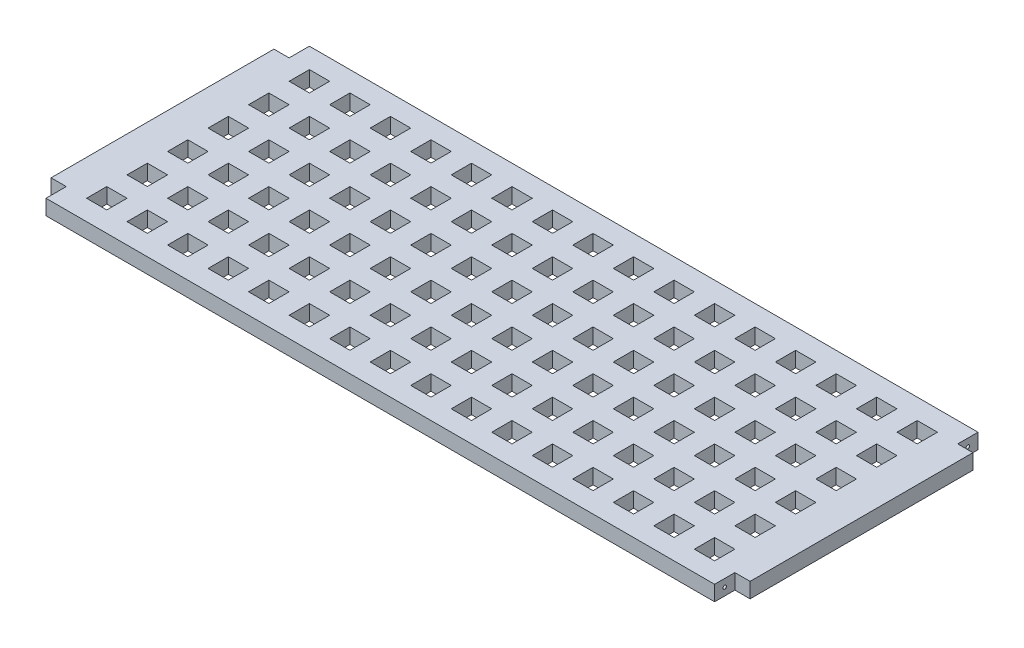
SolidWorks part; units mm, degrees
ref_plane "Front Plane" through (0, 0, 0) normal (0, 0, 1) x (1, 0, 0)
ref_plane "Top Plane" through (0, 0, 0) normal (0, 1, 0) x (1, 0, 0)
ref_plane "Right Plane" through (0, 0, 0) normal (1, 0, 0) x (0, 0, -1)
sketch "Sketch1" plane through (0, 0, 0) normal (0, 1, 0) x (1, 0, 0)
  line L0 (-373.3767, 133.8437) -> (-358.3767, 133.8437)
  line L1 (-358.3767, 133.8437) -> (-358.3767, 153.8437)
  line L2 (-358.3767, 153.8437) -> (301.6233, 153.8437)
  line L3 (301.6233, 153.8437) -> (301.6233, 133.8437)
  line L4 (301.6233, 133.8437) -> (316.6233, 133.8437)
  line L5 (316.6233, 133.8437) -> (316.6233, -86.1563)
  line L6 (316.6233, -86.1563) -> (301.6233, -86.1563)
  line L7 (301.6233, -86.1563) -> (301.6233, -106.1563)
  line L8 (301.6233, -106.1563) -> (-358.3767, -106.1563)
  line L9 (-358.3767, -106.1563) -> (-358.3767, -86.1563)
  line L10 (-358.3767, -86.1563) -> (-373.3767, -86.1563)
  line L11 (-373.3767, -86.1563) -> (-373.3767, 133.8437)
  dimension "D1" = 660
  dimension "D2" = 20
  dimension "D3" = 20
  dimension "D4" = 15
  dimension "D5" = 15
  dimension "D6" = 220
  dimension "D7" = 15
  dimension "D8" = 20
  dimension "D9" = 220
  dimension "D10" = 660
extrude "Boss-Extrude2" add sketch "Sketch1" against normal blind 15
sketch "Sketch2" plane through (0, 0, 0) normal (0, 1, 0) x (1, 0, 0)
  line L0 (301.6233, 153.8437) -> (-358.3767, 153.8437) construction
  line L1 (-338.3767, 133.8437) -> (-318.3767, 133.8437)
  line L2 (-338.3767, 133.8437) -> (-338.3767, 113.8437)
  line L3 (-338.3767, 113.8437) -> (-318.3767, 113.8437)
  line L4 (-318.3767, 133.8437) -> (-318.3767, 113.8437)
  line L5 (-373.3767, 133.8437) -> (-373.3767, -86.1563) construction
  dimension "D1" = 20
  dimension "D2" = 35
  dimension "D3" = 20
  dimension "D4" = 20
extrude "Cut-Extrude1" cut sketch "Sketch2" against normal blind 15
pattern_linear "LPattern1" count 16 spacing 40 along (1, 0, 0) count 6 spacing 40 along (0, 0, 1) of "Cut-Extrude1"
sketch "Sketch7" plane through (301.6233, 0, 0) normal (1, 0, 0) x (0, 0, -1)
  line L0 (153.8437, -15) -> (153.8437, 0) construction
  line L1 (153.8437, 0) -> (133.8437, 0) construction
  line L2 (-106.1563, -15) -> (-106.1563, 0) construction
  point P1 (143.8437, -7.5)
  point P2 (-96.1563, -7.5)
  point P3 (143.8437, -7.5)
  point P6 (153.8437, -7.5)
  dimension "D1" = 10
  dimension "D2" = 7.5
  dimension "D3" = 10
hole_wizard "M3 Clearance Hole2" positions "3DSketch2" profile "Sketch9" hole size "M3" standard "ANSI Metric"
sketch3d "3DSketch2"
  point P1 (301.6233, -7.5, -143.8437)
  point P4 (301.6233, -7.5, 96.1563)
sketch "Sketch9" plane through (301.6233, -7.5, -143.8437) normal (0, 1, 0) x (0, 0, -1)
  line L0 (0, 0) -> (0, 15)
  line L1 (0, 15) -> (1.7, 13.9785)
  line L2 (1.7, 13.9785) -> (1.7, 0.025)
  line L3 (1.7, 0.025) -> (1.725, 0)
  line L5 (1.725, 0) -> (0, 0)
  line L6 (-1.7, 0.025) -> (-1.725, 0) construction
  line L10 (0, 15) -> (-1.7, 13.9785) construction
  line L11 (0, -6.35) -> (0, 107.95) construction
  dimension "Hole Dia." = 3.4
  dimension "Hole Depth" = 15
  dimension "Near C'Sink Dia." = 3.45
  dimension "Near C'Sink Angle" = 90
  dimension "Drill Angle" = 118
sketch "Sketch10" plane through (-358.3767, 0, 0) normal (-1, 0, 0) x (0, 0, 1)
  point P0 (-143.8437, -7.5)
  point P1 (96.1563, -7.5)
  point P3 (0, 0)
  point P5 (0, 0)
hole_wizard "M3 Clearance Hole3" positions "3DSketch3" profile "Sketch11" hole size "M3" standard "ANSI Metric"
sketch3d "3DSketch3"
  point P0 (-225.5725, 7.6572, 0)
  point P3 (-358.3767, -7.5, 96.1563)
  point P8 (-358.3767, -7.5, -143.8437)
sketch "Sketch11" plane through (-358.3767, -7.5, -143.8437) normal (0, 1, 0) x (0, 0, 1)
  line L0 (0, 0) -> (0, 15)
  line L1 (0, 15) -> (1.7, 13.9785)
  line L2 (1.7, 13.9785) -> (1.7, 0.025)
  line L3 (1.7, 0.025) -> (1.725, 0)
  line L5 (1.725, 0) -> (0, 0)
  line L6 (-1.7, 0.025) -> (-1.725, 0) construction
  line L10 (0, 15) -> (-1.7, 13.9785) construction
  line L11 (0, -6.35) -> (0, 107.95) construction
  dimension "Hole Dia." = 3.4
  dimension "Hole Depth" = 15
  dimension "Near C'Sink Dia." = 3.45
  dimension "Near C'Sink Angle" = 90
  dimension "Drill Angle" = 118
